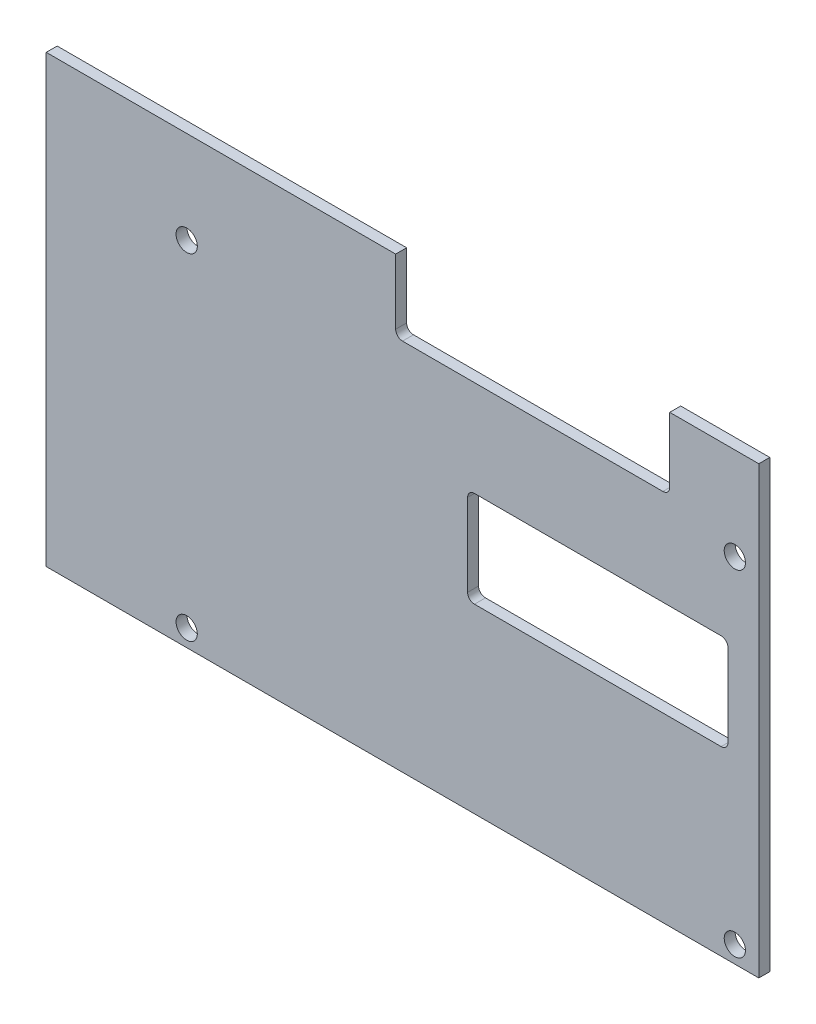
SolidWorks part; units mm, degrees
ref_plane "Спереди" through (0, 0, 0) normal (0, 0, 1) x (1, 0, 0)
ref_plane "Сверху" through (0, 0, 0) normal (0, 1, 0) x (1, 0, 0)
ref_plane "Справа" through (0, 0, 0) normal (1, 0, 0) x (0, 0, -1)
sketch "Эскиз1" plane through (0, 0, 0) normal (0, 0, 1) x (1, 0, 0)
  line L0 (0, 65) -> (51, 65)
  line L1 (0, 0) -> (104, 0)
  line L2 (0, 0) -> (0, 65)
  line L3 (51, 65) -> (51, 55.5)
  line L4 (104, 0) -> (104, 65)
  line L5 (52, 54.5) -> (90, 54.5)
  line L6 (91, 55.5) -> (91, 65)
  line L7 (91, 65) -> (104, 65)
  line L9 (62.5, 40.5) -> (98.5, 40.5)
  line L10 (61.5, 39.5) -> (61.5, 27.5)
  line L11 (62.5, 26.5) -> (98.5, 26.5)
  line L12 (99.5, 39.5) -> (99.5, 27.5)
  circle A0 centre (20.5, 51.5) radius 1.55
  circle A1 centre (100.5, 51.5) radius 1.55
  circle A2 centre (100.5, 2.5) radius 1.55
  circle A3 centre (20.5, 2.5) radius 1.55
  arc A4 (62.5, 40.5) -> (61.5, 39.5) centre (62.5, 39.5) ccw
  arc A5 (99.5, 39.5) -> (98.5, 40.5) centre (98.5, 39.5) ccw
  arc A6 (91, 55.5) -> (90, 54.5) centre (90, 55.5) cw
  arc A7 (52, 54.5) -> (51, 55.5) centre (52, 55.5) cw
  arc A8 (99.5, 27.5) -> (98.5, 26.5) centre (98.5, 27.5) cw
  arc A9 (62.5, 26.5) -> (61.5, 27.5) centre (62.5, 27.5) cw
  dimension "D6" = 49
  dimension "D8" = 65
  dimension "D9" = 2.5
  dimension "D10" = 3.1
  dimension "D2" = 80
  dimension "D5" = 3.5
  dimension "D11" = 1
  dimension "D12" = 38
  dimension "D13" = 14
  dimension "D14" = 1
  dimension "D17" = 1
  dimension "D16" = 24
  dimension "D3" = 104
  dimension "D4" = 13
  dimension "D7" = 54.5
  dimension "D15" = 40
extrude "Бобышка-Вытянуть1" add sketch "Эскиз1" along normal blind 1.6
